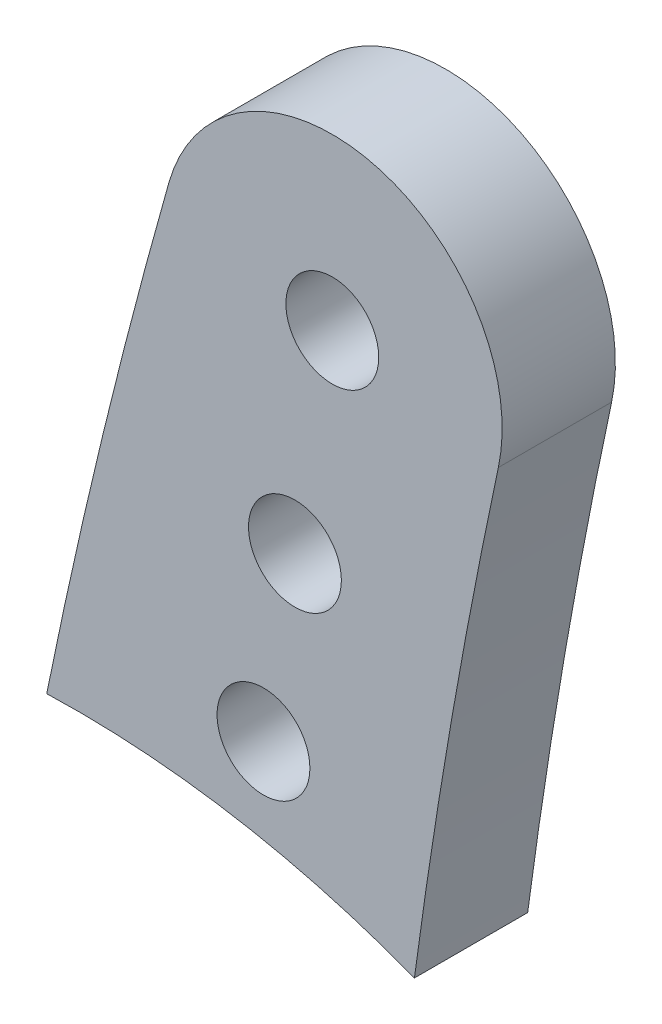
SolidWorks part; units mm, degrees
material "Acrílico (Impacto medio-alto)"
ref_plane "Piano frontale" through (0, 0, 0) normal (0, 0, 1) x (1, 0, 0)
ref_plane "Piano superiore" through (0, 0, 0) normal (0, 1, 0) x (1, 0, 0)
ref_plane "Piano destro" through (0, 0, 0) normal (1, 0, 0) x (0, 0, -1)
sketch "Schizzo1" plane through (0, 0, 0) normal (0, 0, 1) x (1, 0, 0)
  line L0 (-0.3094, 139.9997) -> (-1.9591, 130.644) construction
  line L1 (-1.9591, 130.644) -> (5.4726, 130.644) construction
  circle A0 centre (0, 0) radius 2.05 construction
  circle A1 centre (-0.3094, 139.9997) radius 2.05
  arc A2 (7.024, 138.4277) -> (-7.5254, 142.0442) centre (-0.3094, 139.9997) ccw
  arc A3 (-12.2223, -2.6202) -> (11.9963, 3.5125) centre (0, 0) ccw construction
  arc A4 (-7.5254, 142.0442) -> (-12.2223, -2.6202) centre (281.1129, 60.2643) ccw construction
  arc A5 (7.024, 138.4277) -> (11.9963, 3.5125) centre (275.9157, 80.7886) ccw construction
  arc A6 (-7.5254, 142.0442) -> (-12.9192, 119.8055) centre (281.1129, 60.2643) ccw
  arc A7 (7.024, 138.4277) -> (3.3171, 117.0519) centre (275.9157, 80.7886) ccw
  arc A8 (-12.9192, 119.8055) -> (3.3171, 117.0519) centre (-11.5885, 78.4072) cw
  circle A9 centre (-1.9591, 130.644) radius 2.05
  circle A10 centre (-3.3483, 122.7655) radius 2.05
  dimension "D1" = 4.1
  dimension "D2" = 80
  dimension "D4" = 15
  dimension "D5" = 25
  dimension "D6" = 600
  dimension "D7" = 550
  dimension "D9" = 4.1
  dimension "D10" = 8
  dimension "D3" = 140
  dimension "D8" = 9.5
extrude "Estrusione-Estrusione1" add sketch "Schizzo1" along normal blind 5
